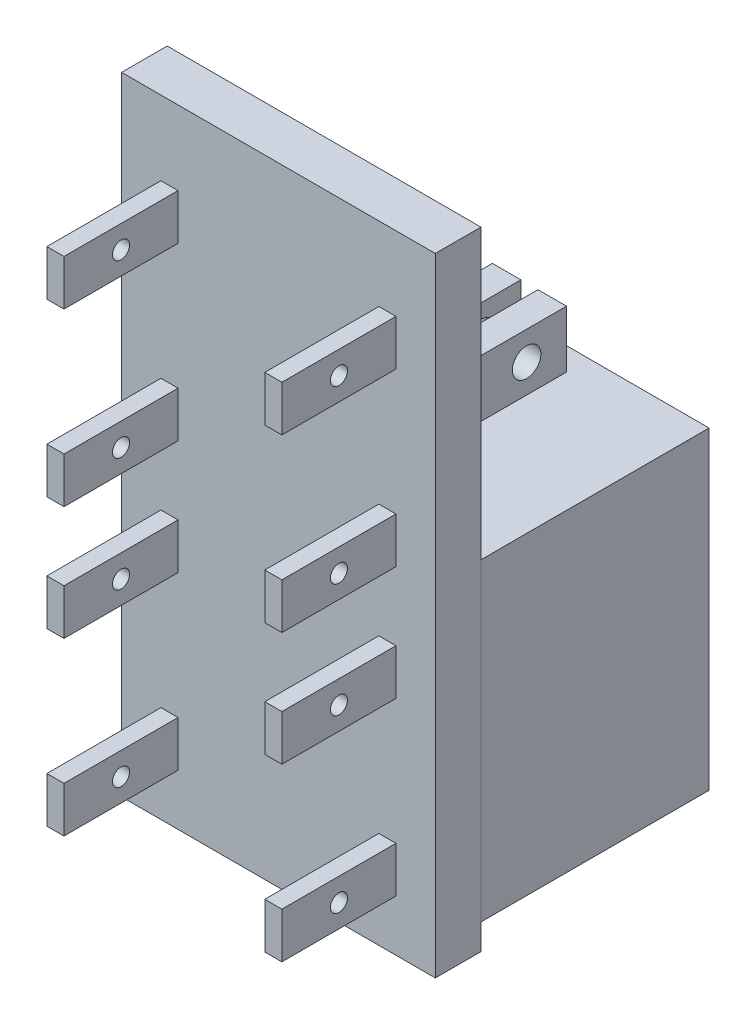
SolidWorks part; units mm, degrees
ref_plane "Plan de face" through (0, 0, 0) normal (0, 0, 1) x (1, 0, 0)
ref_plane "Plan de dessus" through (0, 0, 0) normal (0, 1, 0) x (1, 0, 0)
ref_plane "Plan de droite" through (0, 0, 0) normal (1, 0, 0) x (0, 0, -1)
sketch "Sketch1" plane through (0, 0, 0) normal (0, 0, 1) x (1, 0, 0)
  line L0 (-21, 0) -> (21, 0)
  line L1 (21, 0) -> (21, 42)
  line L2 (21, 42) -> (1.5, 42)
  line L3 (1.5, 42) -> (1.5, 58.5)
  line L4 (1.5, 58.5) -> (6.5, 58.5)
  line L5 (6.5, 58.5) -> (6.5, 48.5)
  line L6 (6.5, 48.5) -> (27.5, 48.5)
  line L7 (27.5, 48.5) -> (27.5, -6.5)
  line L8 (27.5, -6.5) -> (-27.5, -6.5)
  line L9 (0, 0) -> (0, -28.5179) construction
  line L10 (-27.5, 48.5) -> (-27.5, -6.5)
  line L11 (-6.5, 48.5) -> (-27.5, 48.5)
  line L12 (-6.5, 58.5) -> (-6.5, 48.5)
  line L13 (-1.5, 58.5) -> (-6.5, 58.5)
  line L14 (-1.5, 42) -> (-1.5, 58.5)
  line L15 (-21, 42) -> (-1.5, 42)
  line L16 (-21, 0) -> (-21, 42)
  point P13 (0, -6.5)
  dimension "D1" = 55
  dimension "D2" = 42
  dimension "D3" = 6.5
  dimension "D4" = 6.5
  dimension "D5" = 3
  dimension "D6" = 10
  dimension "D7" = 5
  dimension "D8" = 42
extrude "Boss-Extrude1" add sketch "Sketch1" along normal blind 40 contours L2 L3 L4 L5 L6 L7 L8 L10 L11 L12 L13 L14 L15 L16 L0 L1
sketch "Sketch2" plane through (-6.5, 0, 0) normal (-1, 0, 0) x (0, 0, 1)
  line L0 (20, 58.5) -> (20, 48.5) construction
  line L1 (40, 58.5) -> (0, 58.5) construction
  line L2 (40, 48.5) -> (0, 48.5) construction
  circle A0 centre (11, 53.5) radius 2.5
  circle A1 centre (29, 53.5) radius 2.5
  dimension "D1" = 5
  dimension "D2" = 9
  dimension "D3" = 5
extrude "Cut-Extrude1" cut sketch "Sketch2" against normal up to surface (13 mm away) contours A0
sketch "Sketch3" plane through (0, 0, 0) normal (0, 0, -1) x (-1, 0, 0)
  line L0 (20.5, -6.5) -> (19.1705, -5.0058)
  line L1 (-27.5, -6.5) -> (27.5, -6.5) construction
  line L2 (16.9293, -4) -> (-3.9293, -4)
  line L4 (-7.5, -6.5) -> (-6.1705, -5.0058)
  line L5 (20.5, -6.5) -> (-7.5, -6.5)
  arc A0 (19.1705, -5.0058) -> (16.9293, -4) centre (16.9293, -7) ccw
  arc A1 (-6.1705, -5.0058) -> (-3.9293, -4) centre (-3.9293, -7) cw
  point P11 (18.2756, -4)
  point P14 (-5.2756, -4)
  dimension "D1" = 3
  dimension "D2" = 2.5
  dimension "D3" = 20
  dimension "D4" = 2
  dimension "D5" = 7
  dimension "D6" = 2
extrude "Cut-Extrude2" cut sketch "Sketch3" against normal blind 10
sketch "Sketch6" plane through (0, 0, 40) normal (0, 0, 1) x (1, 0, 0)
  line L0 (27.5, 48.5) -> (27.5, -6.5) construction
  line L1 (-27.5, -11) -> (27.5, -11)
  line L2 (-27.5, -11) -> (-27.5, 99)
  line L3 (-27.5, 99) -> (27.5, 99)
  line L4 (27.5, -11) -> (27.5, 99)
  line L7 (27.5, -6.5) -> (-27.5, -6.5) construction
  dimension "D1" = 4.5
  dimension "D2" = 110
  dimension "D3" = 55
extrude "Boss-Extrude8" add sketch "Sketch6" along normal blind 8 separate body
sketch "Sketch7" plane through (-6.5, 0, 0) normal (-1, 0, 0) x (0, 0, 1)
  line L0 (40, 48.5) -> (0, 48.5) construction
  line L1 (40, 58.5) -> (36, 58.5)
  line L2 (40, 58.5) -> (40, 48.5)
  line L3 (40, 48.5) -> (36, 48.5)
  line L4 (36, 58.5) -> (36, 48.5)
  line L5 (20, 58.5) -> (20, 48.5) construction
  line L6 (40, 58.5) -> (0, 58.5) construction
  line L7 (40, 48.5) -> (0, 48.5) construction
  line L8 (0, 48.5) -> (4, 48.5)
  line L9 (0, 58.5) -> (0, 48.5)
  line L10 (0, 58.5) -> (4, 58.5)
  line L11 (4, 58.5) -> (4, 48.5)
  dimension "D1" = 4
extrude "Cut-Extrude3" cut sketch "Sketch7" against normal up to surface (13 mm away) up to face at (6.5, 56, 29)
ref_plane "Plane1" through (16.5, 0, 0) normal (1, 0, 0) x (0, 0, -1)
sketch "Sketch10" [suppressed] plane through (16.5, 0, 0) normal (1, 0, 0) x (0, 0, -1)
  line L0 (-40, 68.5) -> (-20, 48.5)
  line L1 (-40, -11) -> (-40, 99) construction
  line L2 (-40, 48.5) -> (0, 48.5) construction
  dimension "D1" = 20
  dimension "D2" = 20
ref_plane "Plane3" through (0, 0, 0) normal (1, 0, 0) x (0, 0, -1)
sketch "Sketch11" plane through (0, 0, 48) normal (0, 0, 1) x (1, 0, 0)
  line L0 (-27.5, 99) -> (-27.5, -11) construction
  line L1 (-20.6, 86) -> (-17.6, 86)
  line L2 (-20.6, 86) -> (-20.6, 78)
  line L3 (-20.6, 78) -> (-17.6, 78)
  line L4 (-17.6, 86) -> (-17.6, 78)
  line L5 (27.5, 99) -> (-27.5, 99) construction
  line L6 (-27.5, 42) -> (5.7373, 42) construction
  line L7 (27.5, -11) -> (27.5, 99) construction
  line L8 (-17.6, -2) -> (-17.6, 6)
  line L9 (-20.6, 6) -> (-17.6, 6)
  line L10 (-20.6, -2) -> (-20.6, 6)
  line L11 (-20.6, -2) -> (-17.6, -2)
  line L12 (20.6, -2) -> (17.6, -2)
  line L13 (20.6, -2) -> (20.6, 6)
  line L14 (20.6, 6) -> (17.6, 6)
  line L15 (17.6, -2) -> (17.6, 6)
  line L16 (17.6, 86) -> (17.6, 78)
  line L17 (20.6, 78) -> (17.6, 78)
  line L18 (20.6, 86) -> (20.6, 78)
  line L19 (20.6, 86) -> (17.6, 86)
  line L21 (-17.5, 67) -> (-25.8621, 67) construction
  line L22 (-17.5, 17) -> (-27.5, 17) construction
  line L23 (20.6, 48) -> (17.6, 48)
  line L24 (20.6, 48) -> (20.6, 56)
  line L25 (20.6, 56) -> (17.6, 56)
  line L26 (17.6, 48) -> (17.6, 56)
  line L27 (-17.6, 48) -> (-17.6, 56)
  line L28 (-20.6, 56) -> (-17.6, 56)
  line L29 (-20.6, 48) -> (-20.6, 56)
  line L30 (-20.6, 48) -> (-17.6, 48)
  line L31 (17.6, 36) -> (17.6, 28)
  line L32 (20.6, 28) -> (17.6, 28)
  line L33 (20.6, 36) -> (20.6, 28)
  line L34 (20.6, 36) -> (17.6, 36)
  line L35 (-20.6, 36) -> (-17.6, 36)
  line L36 (-20.6, 36) -> (-20.6, 28)
  line L37 (-20.6, 28) -> (-17.6, 28)
  line L38 (-17.6, 36) -> (-17.6, 28)
  dimension "D1" = 8
  dimension "D2" = 6.9
  dimension "D3" = 3
  dimension "D4" = 13
  dimension "D5" = 44
  dimension "D6" = 3
  dimension "D7" = 8
  dimension "D8" = 6.9
  dimension "D9" = 13
  dimension "D10" = 6.9
  dimension "D11" = 3
  dimension "D12" = 8
  dimension "D13" = 72
extrude "Boss-Extrude9" add sketch "Sketch11" along normal up to surface (20 mm away)
sketch "Sketch12" plane through (-20.6, 0, 0) normal (-1, 0, 0) x (0, 0, 1)
  line L0 (68, 86) -> (48, 78) construction
  circle A0 centre (58, 82) radius 1.5
  dimension "D1" = 3
extrude "Cut-Extrude4" cut sketch "Sketch12" against normal up to surface (41.2 mm away) up to face at (20.6, 82, 58)
ref_plane "Plane4" through (0, 67, 0) normal (0, -1, 0) x (-1, 0, 0)
ref_plane "Plane6" through (0, 42, 0) normal (0, -1, 0) x (-1, 0, 0)
mirror "Mirror1" about plane through (0, 67, 0) normal (0, -1, 0) of "Cut-Extrude4"
mirror "Mirror2" about plane through (0, 42, 0) normal (0, -1, 0) of "Cut-Extrude4"
mirror "Mirror3" about plane through (0, 42, 0) normal (0, -1, 0) of "Mirror1"
